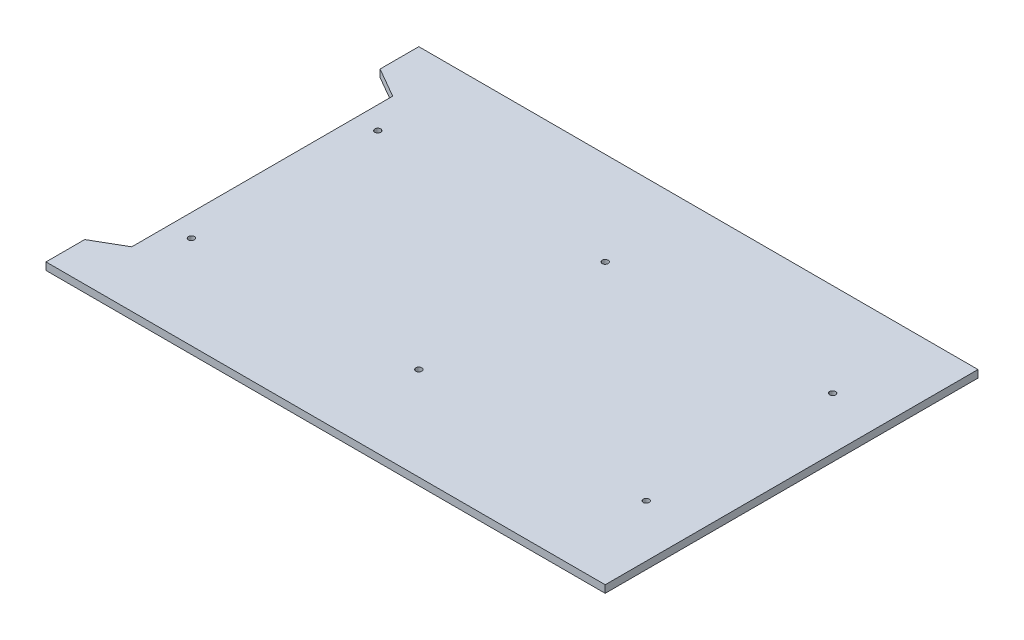
SolidWorks part; units mm, degrees
material "Stainless Steel (ferritic)"
ref_plane "Front Plane" through (0, 0, 0) normal (0, 0, 1) x (1, 0, 0)
ref_plane "Top Plane" through (0, 0, 0) normal (0, 1, 0) x (1, 0, 0)
ref_plane "Right Plane" through (0, 0, 0) normal (1, 0, 0) x (0, 0, -1)
sketch "Sketch1" plane through (0, 0, 0) normal (0, 1, 0) x (1, 0, 0)
  line L1 (-375, 250) -> (375, 250)
  line L2 (-375, 250) -> (-375, -250)
  line L3 (-375, -250) -> (375, -250)
  line L4 (375, 250) -> (375, -250)
  line L5 (-375, 250) -> (375, -250) construction
  line L6 (-375, -250) -> (375, 250) construction
  point P0 (0, 0)
  dimension "D1" = 750
  dimension "D2" = 500
extrude "Boss-Extrude1" add sketch "Sketch1" along normal blind 10
sketch "Sketch2" plane through (0, 10, 0) normal (0, 1, 0) x (1, 0, 0)
  line L0 (375, 250) -> (-375, 250) construction
  line L1 (375, -250) -> (375, 250) construction
  circle A0 centre (305, 125) radius 4
  dimension "D1" = 125
  dimension "D2" = 70
  dimension "D3" = 8
extrude "Cut-Extrude1" cut sketch "Sketch2" against normal blind 10
sketch "Sketch3" plane through (0, 10, 0) normal (0, 1, 0) x (1, 0, 0)
  line L0 (-375, -250) -> (375, -250) construction
  line L1 (375, -250) -> (375, 250) construction
  circle A0 centre (305, -125) radius 4
  dimension "D1" = 125
  dimension "D2" = 70
  dimension "D3" = 8
extrude "Cut-Extrude2" cut sketch "Sketch3" against normal blind 10
sketch "Sketch4" plane through (0, 10, 0) normal (0, 1, 0) x (1, 0, 0)
  line L0 (375, -250) -> (375, 250) construction
  line L1 (375, 250) -> (-375, 250) construction
  circle A0 centre (0, 125) radius 4
  dimension "D1" = 8
  dimension "D2" = 375
  dimension "D3" = 125
extrude "Cut-Extrude3" cut sketch "Sketch4" against normal blind 10
sketch "Sketch5" plane through (0, 10, 0) normal (0, 1, 0) x (1, 0, 0)
  circle A0 centre (0, -125) radius 4
extrude "Cut-Extrude4" cut sketch "Sketch5" against normal blind 10
sketch "Sketch6" plane through (0, 10, 0) normal (0, 1, 0) x (1, 0, 0)
  line L0 (-375, 250) -> (-375, -250) construction
  line L1 (375, 250) -> (-375, 250) construction
  circle A0 centre (-305, 125) radius 4
  dimension "D1" = 70
  dimension "D2" = 125
  dimension "D3" = 8
extrude "Cut-Extrude5" cut sketch "Sketch6" against normal blind 10
sketch "Sketch7" plane through (0, 10, 0) normal (0, 1, 0) x (1, 0, 0)
  line L0 (-375, 250) -> (-375, -250) construction
  line L1 (-375, -250) -> (375, -250) construction
  circle A0 centre (-305, -125) radius 4
  dimension "D1" = 8
  dimension "D2" = 70
  dimension "D3" = 125
extrude "Cut-Extrude6" cut sketch "Sketch7" against normal blind 10 contours A0
sketch "Sketch9" plane through (0, 10, 0) normal (0, 1, 0) x (1, 0, 0)
  line L0 (-375, 250) -> (0, 250) construction
  line L1 (375, 250) -> (-375, 250) construction
  line L2 (-187.5, 250) -> (-187.5, -250) construction
  line L3 (-375, -250) -> (375, -250) construction
sketch "Sketch10" plane through (0, 10, 0) normal (0, 1, 0) x (1, 0, 0)
  line L0 (-375, 0) -> (-322.1323, 0) construction
  line L1 (-375, 250) -> (-375, -250) construction
  line L2 (-335, 175) -> (-335, -175)
  line L3 (-335, 175) -> (-375, 198.094)
  line L4 (-335, -175) -> (-375, -198.094)
  line L5 (-375, 198.094) -> (-375, -198.094)
  point P10 (-335, 0)
  dimension "D1" = 175
  dimension "D2" = 40
  dimension "D3" = 120
extrude "Cut-Extrude7" cut sketch "Sketch10" against normal up to next
